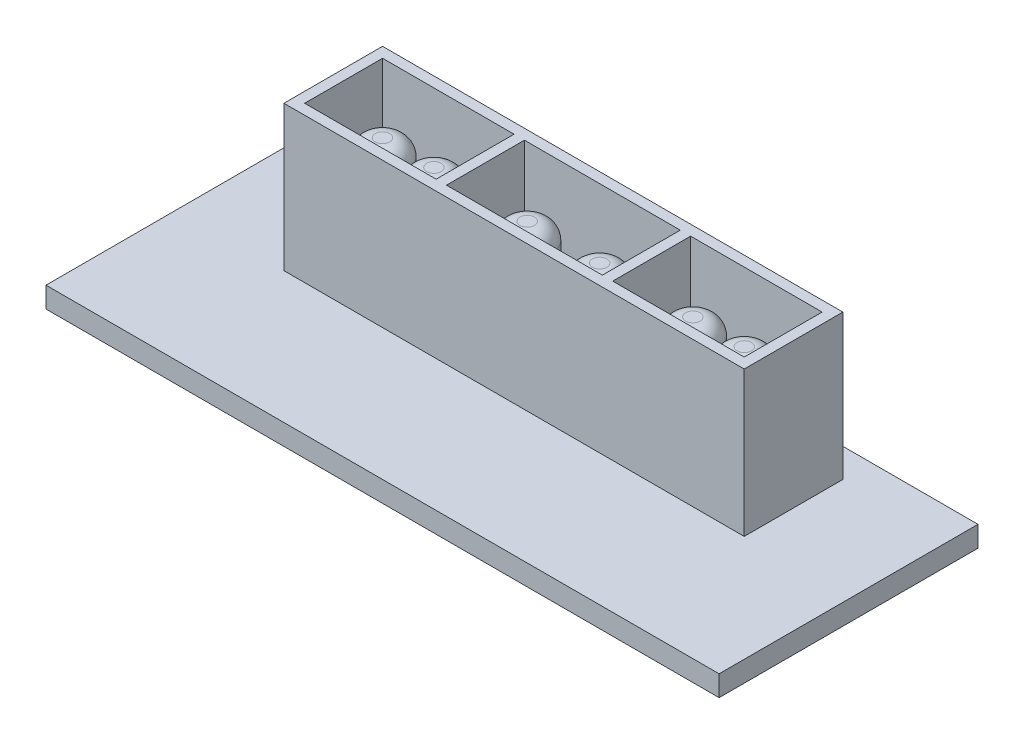
SolidWorks part; units mm, degrees
ref_plane "Front Plane" through (0, 0, 0) normal (0, 0, 1) x (1, 0, 0)
ref_plane "Top Plane" through (0, 0, 0) normal (0, 1, 0) x (1, 0, 0)
ref_plane "Right Plane" through (0, 0, 0) normal (1, 0, 0) x (0, 0, -1)
sketch "Sketch1" plane through (0, 0, 0) normal (0, 1, 0) x (1, 0, 0)
  line L1 (0, 0) -> (-65, 0)
  line L2 (0, 0) -> (0, 25)
  line L3 (0, 25) -> (-65, 25)
  line L4 (-65, 0) -> (-65, 25)
  dimension "D1" = 65
  dimension "D2" = 25
extrude "Boss-Extrude1" add sketch "Sketch1" along normal blind 2
sketch "Sketch2" plane through (0, 2, 0) normal (0, 1, 0) x (1, 0, 0)
  line L1 (-54.725, 22.225) -> (-10.275, 22.225)
  line L2 (-54.725, 22.225) -> (-54.725, 12.7)
  line L3 (-54.725, 12.7) -> (-10.275, 12.7)
  line L4 (-10.275, 22.225) -> (-10.275, 12.7)
  line L5 (-32.5, 0) -> (-32.5, 22.225) construction
  line L6 (-65, 0) -> (0, 0) construction
  line L7 (-53.725, 21.225) -> (-41.025, 21.225)
  line L8 (-11.275, 21.225) -> (-11.275, 13.7)
  line L9 (-53.725, 13.7) -> (-41.025, 13.7)
  line L10 (-53.725, 21.225) -> (-53.725, 13.7)
  line L11 (-24.975, 21.225) -> (-24.975, 13.7)
  line L12 (-23.975, 13.7) -> (-11.275, 13.7)
  line L13 (-41.025, 21.225) -> (-41.025, 13.7)
  line L14 (-23.975, 21.225) -> (-11.275, 21.225)
  line L15 (-40.025, 21.225) -> (-40.025, 13.7)
  line L16 (-23.975, 21.225) -> (-23.975, 13.7)
  line L17 (-40.025, 21.225) -> (-24.975, 21.225)
  line L18 (-40.025, 13.7) -> (-24.975, 13.7)
  line L19 (-53.725, 21.225) -> (-11.275, 21.225) construction
  line L21 (-53.725, 13.7) -> (-11.275, 13.7) construction
  point P4 (-32.5, 22.225)
  dimension "D1" = 9.525
  dimension "D2" = 44.45
  dimension "D3" = 12.7
  dimension "D5" = 1
  dimension "D6" = 12.7
  dimension "D4" = 1
extrude "Boss-Extrude2" add sketch "Sketch2" along normal blind 14
sketch "Sketch3" plane through (0, 2, 0) normal (0, 1, 0) x (1, 0, 0)
  line L0 (-54.725, 17.4625) -> (-10.275, 17.4625) construction
  line L1 (-54.725, 22.225) -> (-54.725, 12.7) construction
  line L2 (-10.275, 12.7) -> (-10.275, 22.225) construction
  line L3 (-32.5, 21.225) -> (-32.5, 13.7) construction
  line L4 (-24.975, 21.225) -> (-40.025, 21.225) construction
  line L5 (-40.025, 13.7) -> (-24.975, 13.7) construction
  circle A0 centre (-36, 17.4625) radius 2.3
  circle A1 centre (-49.97, 17.4625) radius 2.3
  circle A2 centre (-19.998, 17.4625) radius 2.3
  circle A3 centre (-29, 17.4625) radius 2.3
  circle A4 centre (-15.03, 17.4625) radius 2.3
  circle A5 centre (-45.002, 17.4625) radius 2.3
  dimension "D1" = 3.5
  dimension "D3" = 4.6
  dimension "D2" = 2
  dimension "D4" = 2
  dimension "D5" = 2
  dimension "D6" = 2
extrude "Boss-Extrude4" add sketch "Sketch3" along normal blind 11.1125
fillet "Fillet2" radius 1.6 6 edges at (-15.03, 13.1125, -19.7625) (-19.998, 13.1125, -15.1625) (-29, 13.1125, -19.7625) (-36, 13.1125, -15.1625) (-45.002, 13.1125, -19.7625) (-49.97, 13.1125, -15.1625)
